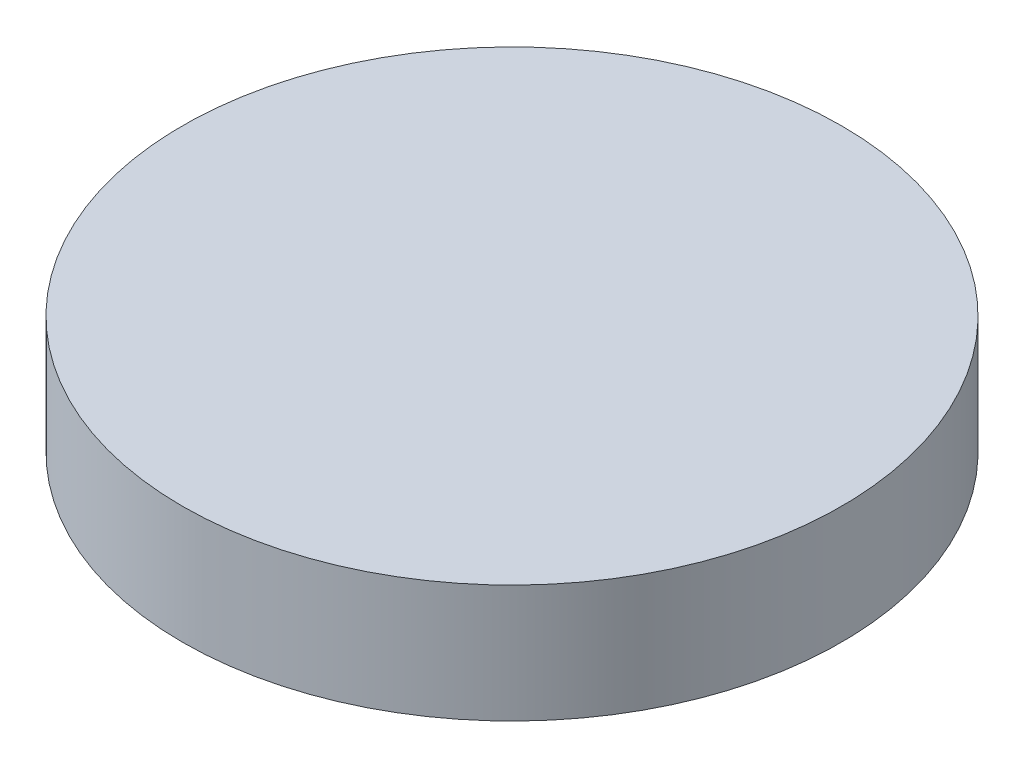
SolidWorks part; units mm, degrees
ref_plane "Ön Düzlem" through (0, 0, 0) normal (0, 0, 1) x (1, 0, 0)
ref_plane "Üst Düzlem" through (0, 0, 0) normal (0, 1, 0) x (1, 0, 0)
ref_plane "Sağ Düzlem" through (0, 0, 0) normal (1, 0, 0) x (0, 0, -1)
sketch "Çizim1" plane through (0, 0, 0) normal (0, 1, 0) x (1, 0, 0)
  circle A0 centre (0, 0) radius 27.985
  dimension "D1" = 55.97
extrude "Yükseklik-Ekstrüzyon1" add sketch "Çizim1" along normal blind 10
